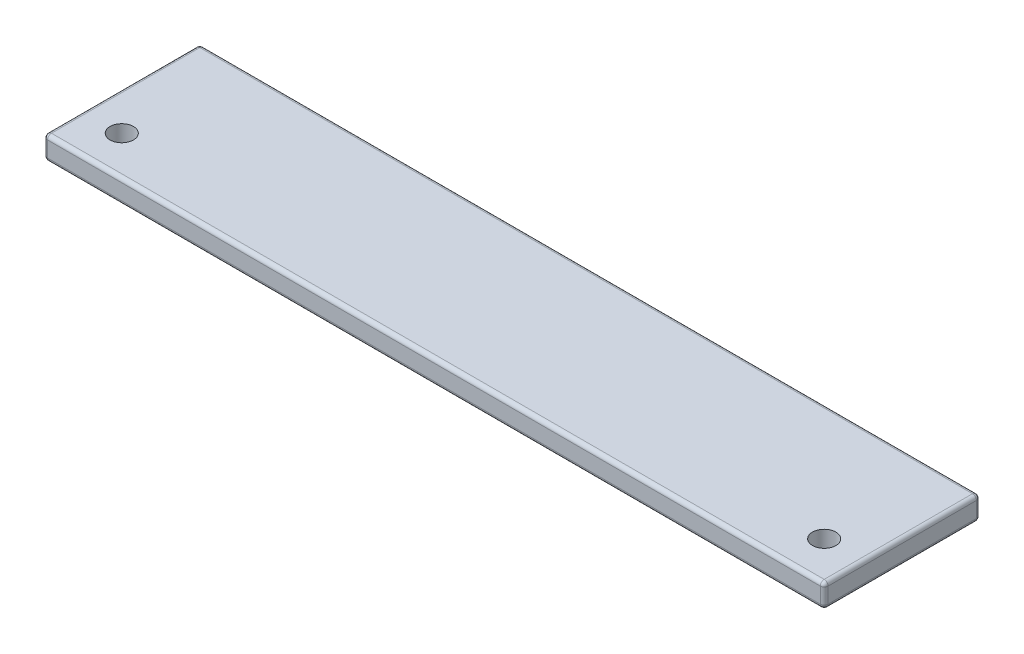
SolidWorks part; units mm, degrees
ref_plane "Front" through (0, 0, 0) normal (0, 0, 1) x (1, 0, 0)
ref_plane "Top" through (0, 0, 0) normal (0, 1, 0) x (1, 0, 0)
ref_plane "Right" through (0, 0, 0) normal (1, 0, 0) x (0, 0, -1)
sketch "Sketch1" plane through (0, 0, 0) normal (0, 1, 0) x (1, 0, 0)
  line L1 (50, -10) -> (-50, -10)
  line L2 (50, -10) -> (50, 10)
  line L3 (50, 10) -> (-50, 10)
  line L4 (-50, -10) -> (-50, 10)
  line L5 (50, -10) -> (-50, 10) construction
  line L6 (50, 10) -> (-50, -10) construction
  point P0 (0, 0)
  dimension "D1" = 100
  dimension "D2" = 20
extrude "Boss-Extrude1" add sketch "Sketch1" along normal blind 3
fillet "Fillet1" radius 0.5 12 edges at (0, 0, 10) (50, 0, 0) (0, 0, -10) (-50, 0, 0) (0, 3, -10) (50, 3, 0) (0, 3, 10) (-50, 3, 0) (50, 1.5, 10) (-50, 1.5, 10) (50, 1.5, -10) (-50, 1.5, -10)
sketch "Sketch2" plane through (0, 0, 0) normal (0, -1, 0) x (1, 0, 0)
  line L0 (50, 9.5) -> (50, -9.5) construction
  line L1 (49.5, -10) -> (-49.5, -10) construction
  circle A0 centre (45, 5) radius 1.5
  dimension "D1" = 3
  dimension "D2" = 5
  dimension "D3" = 15
extrude "Cut-Extrude1" cut sketch "Sketch2" against normal through all
mirror "Mirror1" about plane through (0, 0, 0) normal (1, 0, 0) of "Cut-Extrude1"
